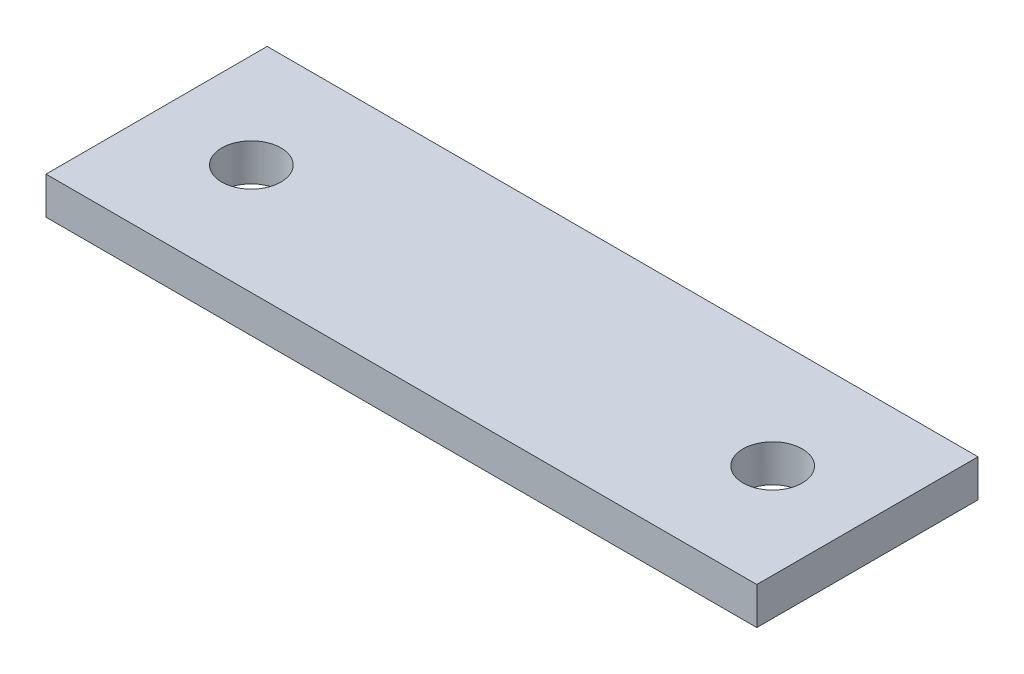
SolidWorks part; units mm, degrees
ref_plane "Front Plane" through (0, 0, 0) normal (0, 0, 1) x (1, 0, 0)
ref_plane "Top Plane" through (0, 0, 0) normal (0, 1, 0) x (1, 0, 0)
ref_plane "Right Plane" through (0, 0, 0) normal (1, 0, 0) x (0, 0, -1)
sketch "Sketch1" plane through (0, 0, 0) normal (0, 1, 0) x (1, 0, 0)
  line L1 (0, 0) -> (60, 0)
  line L2 (0, 0) -> (0, 18.67)
  line L3 (0, 18.67) -> (60, 18.67)
  line L4 (60, 0) -> (60, 18.67)
  dimension "D1" = 60
  dimension "D2" = 18.67
extrude "Boss-Extrude1" add sketch "Sketch1" along normal blind 3.15
sketch "Sketch2" plane through (0, 0, 0) normal (0, -1, 0) x (-1, 0, 0)
  line L0 (-60, 9.335) -> (0, 9.335)
  line L1 (-60, 0) -> (-60, 18.67) construction
  line L2 (0, 18.67) -> (0, 0) construction
  line L3 (0, 9.335) -> (-30, 9.335)
  line L4 (-30, 9.335) -> (-30, 18.67)
  line L5 (-60, 18.67) -> (0, 18.67) construction
hole_wizard "Ø5.0mm Dowel Hole1" positions "Sketch3" profile "Sketch4" hole size "Ø5.0" standard "ANSI Metric" end condition up to next
sketch "Sketch3" plane through (0, 3.15, 0) normal (0, 1, 0) x (1, 0, 0)
  point P0 (8, 9.335)
  point P3 (52, 9.335)
sketch "Sketch4" plane through (8, 3.15, -9.335) normal (1, 0, 0) x (0, 0, 1)
  line L0 (0, 0) -> (0, 3.15)
  line L1 (0, 3.15) -> (2.5, 3.15)
  line L2 (2.5, 3.15) -> (2.5, 0)
  line L5 (2.5, 0) -> (0, 0)
  line L11 (0, -6.35) -> (0, 107.95) construction
  dimension "Thru Hole Dia." = 5
  dimension "Thru Hole Depth" = 3.15
